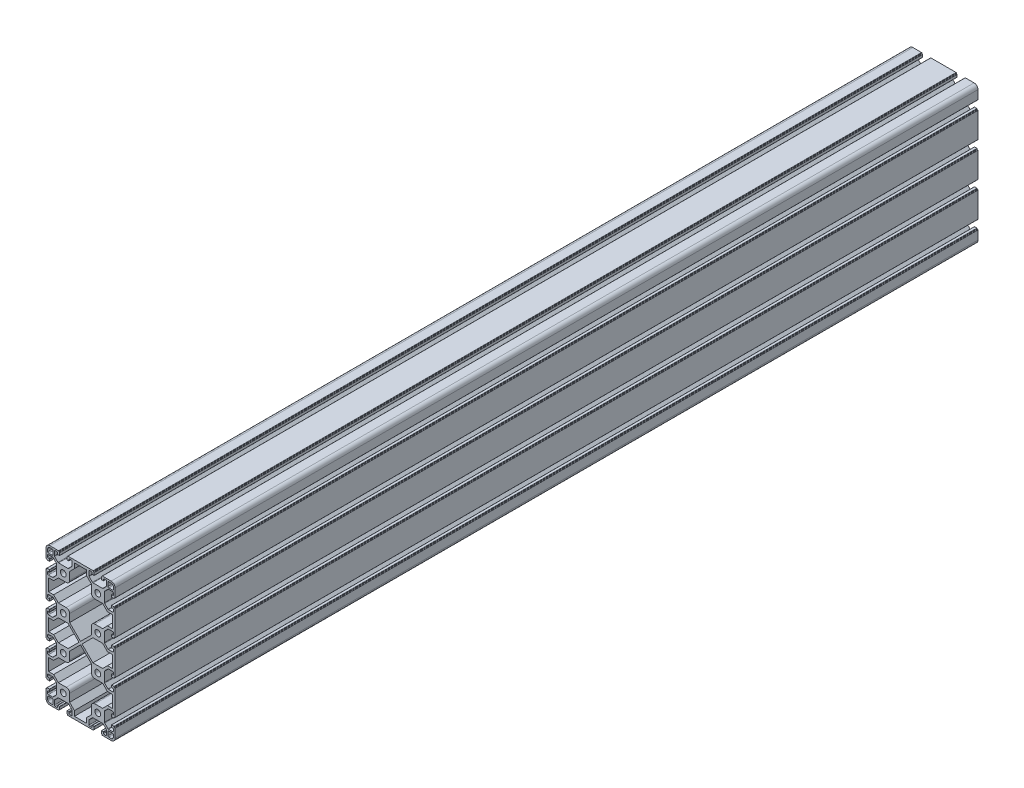
SolidWorks part; units mm, degrees
material "6063 T5"
ref_plane "Спереди" through (0, 0, 0) normal (0, 0, 1) x (1, 0, 0)
ref_plane "Сверху" through (0, 0, 0) normal (0, 1, 0) x (1, 0, 0)
ref_plane "Справа" through (0, 0, 0) normal (1, 0, 0) x (0, 0, -1)
sketch "Эскиз1" plane through (0, 0, 0) normal (0, 0, 1) x (1, 0, 0)
  line L0 (-19.98, 20.5457) -> (20.02, 20.5457) construction
  line L1 (-20, 10.25) -> (-20, 15.5)
  line L2 (-15.5, 20) -> (-10.25, 20)
  line L3 (20, 0) -> (20, 56.8781) construction
  line L4 (-12.8, 11.8) -> (-17, 11.8)
  line L5 (-11.8, 12.8) -> (-11.8, 17)
  line L6 (-12.8, 18) -> (-15.5, 18)
  line L7 (-18, 12.8) -> (-18, 15.5)
  line L20 (0, 0) -> (40, 0) construction
  line L25 (0, 0) -> (0, -120) construction
  line L26 (0, -120) -> (40, -120) construction
  line L31 (40, 0) -> (40, -120) construction
  line L32 (58, 12.8) -> (58, 15.5)
  line L37 (52.8, 18) -> (55.5, 18)
  line L38 (51.8, 12.8) -> (51.8, 17)
  line L43 (52.8, 11.8) -> (57, 11.8)
  line L44 (55.5, 20) -> (50.25, 20)
  line L45 (60, 10.25) -> (60, 15.5)
  line L46 (10.25, 20) -> (29.75, 20)
  line L47 (-20.044, 23.5406) -> (59.956, 23.5406) construction
  line L67 (60, -10.25) -> (60, -50.25) construction
  line L68 (-20, -10.25) -> (-20, -29.75)
  line L72 (-20, -90.25) -> (-20, -109.75)
  line L74 (60, -90.25) -> (60, -109.75)
  line L76 (60, -50.25) -> (60, -69.75)
  line L77 (60, -10.25) -> (60, -29.75)
  line L78 (-20, -50.25) -> (-20, -69.75)
  line L79 (0, -60) -> (23.4541, -60) construction
  line L80 (60, -130.25) -> (60, -135.5)
  line L81 (55.5, -140) -> (50.25, -140)
  line L82 (51.8, -132.8) -> (51.8, -137)
  line L83 (52.8, -131.8) -> (57, -131.8)
  line L84 (58, -132.8) -> (58, -135.5)
  line L85 (52.8, -138) -> (55.5, -138)
  line L86 (10.25, -140) -> (29.75, -140)
  line L87 (-12.8, -138) -> (-15.5, -138)
  line L88 (-18, -132.8) -> (-18, -135.5)
  line L89 (-12.8, -131.8) -> (-17, -131.8)
  line L90 (-11.8, -132.8) -> (-11.8, -137)
  line L91 (-15.5, -140) -> (-10.25, -140)
  line L92 (-20, -130.25) -> (-20, -135.5)
  line L93 (-26.4314, 19.9357) -> (-26.4314, -140.0643) construction
  line L94 (27.0645, 17) -> (12.9355, 17)
  line L95 (12.9355, 17) -> (12.9355, 11.2)
  line L96 (12.9355, 11.2) -> (7.4, 5.6645)
  line L97 (7.4, 5.6645) -> (7.4, -3.4)
  line L98 (3.4, -7.4) -> (-5.6645, -7.4)
  line L99 (-5.6645, -7.4) -> (-11.2, -12.9355)
  line L100 (-11.2, -12.9355) -> (-17, -12.9355)
  line L101 (-17, -12.9355) -> (-17, -27.0645)
  line L102 (-17, -20) -> (21.7241, -20) construction
  line L103 (-11.2, -27.0645) -> (-17, -27.0645)
  line L104 (-5.6645, -32.6) -> (-11.2, -27.0645)
  line L105 (3.4, -32.6) -> (-5.6645, -32.6)
  line L106 (7.4, -45.6645) -> (7.4, -36.6)
  line L107 (7.4, -45.6645) -> (20, -58.2645)
  line L108 (32.6, -45.6645) -> (20, -58.2645)
  line L109 (32.6, -45.6645) -> (32.6, -36.6)
  line L110 (36.6, -32.6) -> (45.6645, -32.6)
  line L111 (45.6645, -32.6) -> (51.2, -27.0645)
  line L112 (51.2, -27.0645) -> (57, -27.0645)
  line L113 (57, -12.9355) -> (57, -27.0645)
  line L114 (51.2, -12.9355) -> (57, -12.9355)
  line L115 (45.6645, -7.4) -> (51.2, -12.9355)
  line L116 (36.6, -7.4) -> (45.6645, -7.4)
  line L117 (32.6, 5.6645) -> (32.6, -3.4)
  line L118 (27.0645, 11.2) -> (32.6, 5.6645)
  line L119 (27.0645, 17) -> (27.0645, 11.2)
  line L120 (18.2645, -60) -> (5.6645, -47.4)
  line L121 (5.6645, -47.4) -> (-5.6645, -47.4)
  line L122 (-5.6645, -47.4) -> (-11.2, -52.9355)
  line L123 (-11.2, -52.9355) -> (-17, -52.9355)
  line L124 (-17, -52.9355) -> (-17, -67.0645)
  line L125 (-11.2, -67.0645) -> (-17, -67.0645)
  line L126 (-5.6645, -72.6) -> (-11.2, -67.0645)
  line L127 (5.6645, -72.6) -> (-5.6645, -72.6)
  line L128 (18.2645, -60) -> (5.6645, -72.6)
  line L129 (21.7355, -60) -> (34.3355, -47.4)
  line L130 (34.3355, -47.4) -> (45.6645, -47.4)
  line L131 (45.6645, -47.4) -> (51.2, -52.9355)
  line L132 (51.2, -52.9355) -> (57, -52.9355)
  line L133 (57, -52.9355) -> (57, -67.0645)
  line L134 (51.2, -67.0645) -> (57, -67.0645)
  line L135 (45.6645, -72.6) -> (51.2, -67.0645)
  line L136 (34.3355, -72.6) -> (45.6645, -72.6)
  line L137 (21.7355, -60) -> (34.3355, -72.6)
  line L138 (51.2, -107.0645) -> (57, -107.0645)
  line L139 (45.6645, -112.6) -> (51.2, -107.0645)
  line L140 (36.6, -112.6) -> (45.6645, -112.6)
  line L141 (32.6, -125.6645) -> (32.6, -116.6)
  line L142 (27.0645, -131.2) -> (32.6, -125.6645)
  line L143 (27.0645, -137) -> (27.0645, -131.2)
  line L144 (27.0645, -137) -> (12.9355, -137)
  line L145 (12.9355, -137) -> (12.9355, -131.2)
  line L146 (12.9355, -131.2) -> (7.4, -125.6645)
  line L147 (7.4, -125.6645) -> (7.4, -116.6)
  line L148 (3.4, -112.6) -> (-5.6645, -112.6)
  line L149 (-5.6645, -112.6) -> (-11.2, -107.0645)
  line L150 (-11.2, -107.0645) -> (-17, -107.0645)
  line L151 (-17, -107.0645) -> (-17, -92.9355)
  line L152 (-11.2, -92.9355) -> (-17, -92.9355)
  line L153 (-5.6645, -87.4) -> (-11.2, -92.9355)
  line L154 (3.4, -87.4) -> (-5.6645, -87.4)
  line L155 (7.4, -74.3355) -> (7.4, -83.4)
  line L156 (7.4, -74.3355) -> (20, -61.7355)
  line L157 (32.6, -74.3355) -> (20, -61.7355)
  line L158 (32.6, -74.3355) -> (32.6, -83.4)
  line L159 (36.6, -87.4) -> (45.6645, -87.4)
  line L160 (45.6645, -87.4) -> (51.2, -92.9355)
  line L161 (51.2, -92.9355) -> (57, -92.9355)
  line L162 (57, -107.0645) -> (57, -92.9355)
  arc A0 (-20, 15.5) -> (-15.5, 20) centre (-15.5, 15.5) cw
  arc A1 (-15.5, 18) -> (-18, 15.5) centre (-15.5, 15.5) ccw
  arc A2 (-17, 11.8) -> (-18, 12.8) centre (-17, 12.8) cw
  arc A3 (-12.8, 11.8) -> (-11.8, 12.8) centre (-12.8, 12.8) ccw
  arc A4 (-11.8, 17) -> (-12.8, 18) centre (-12.8, 17) ccw
  circle A5 centre (0, 0) radius 3.4
  circle A6 centre (40, 0) radius 3.4
  arc A24 (51.8, 17) -> (52.8, 18) centre (52.8, 17) cw
  arc A30 (52.8, 11.8) -> (51.8, 12.8) centre (52.8, 12.8) cw
  arc A40 (57, 11.8) -> (58, 12.8) centre (57, 12.8) ccw
  arc A41 (55.5, 18) -> (58, 15.5) centre (55.5, 15.5) cw
  arc A42 (60, 15.5) -> (55.5, 20) centre (55.5, 15.5) ccw
  circle A43 centre (40, -40) radius 3.4
  circle A44 centre (0, -40) radius 3.4
  circle A45 centre (40, -80) radius 3.4
  circle A46 centre (0, -80) radius 3.4
  circle A47 centre (40, -120) radius 3.4
  circle A48 centre (0, -120) radius 3.4
  arc A49 (60, -135.5) -> (55.5, -140) centre (55.5, -135.5) cw
  arc A50 (52.8, -131.8) -> (51.8, -132.8) centre (52.8, -132.8) ccw
  arc A51 (57, -131.8) -> (58, -132.8) centre (57, -132.8) cw
  arc A52 (55.5, -138) -> (58, -135.5) centre (55.5, -135.5) ccw
  arc A53 (51.8, -137) -> (52.8, -138) centre (52.8, -137) ccw
  arc A54 (-15.5, -138) -> (-18, -135.5) centre (-15.5, -135.5) cw
  arc A55 (-17, -131.8) -> (-18, -132.8) centre (-17, -132.8) ccw
  arc A56 (-12.8, -131.8) -> (-11.8, -132.8) centre (-12.8, -132.8) cw
  arc A57 (-11.8, -137) -> (-12.8, -138) centre (-12.8, -137) cw
  arc A58 (-20, -135.5) -> (-15.5, -140) centre (-15.5, -135.5) ccw
  arc A59 (7.4, -3.4) -> (3.4, -7.4) centre (3.4, -3.4) cw
  arc A60 (7.4, -36.6) -> (3.4, -32.6) centre (3.4, -36.6) ccw
  arc A61 (32.6, -36.6) -> (36.6, -32.6) centre (36.6, -36.6) cw
  arc A62 (32.6, -3.4) -> (36.6, -7.4) centre (36.6, -3.4) ccw
  arc A63 (32.6, -116.6) -> (36.6, -112.6) centre (36.6, -116.6) cw
  arc A64 (7.4, -116.6) -> (3.4, -112.6) centre (3.4, -116.6) ccw
  arc A65 (7.4, -83.4) -> (3.4, -87.4) centre (3.4, -83.4) cw
  arc A66 (32.6, -83.4) -> (36.6, -87.4) centre (36.6, -83.4) ccw
  point P5 (0, 0)
  point P42 (40, 0)
  point P151 (20, 17)
  point P158 (-17, -60)
  line B0 (-20, 10.25) -> (-20, 5.4)
  line B1 (-19.7, 5.1) -> (-19.3, 5.1)
  line B2 (-19, 4.8) -> (-19, 4.4)
  line B3 (-18.7, 4.1) -> (-16, 4.1)
  line B4 (-15.7, 4.4) -> (-15.7, 6.3)
  line B5 (-16, 6.6) -> (-17.2, 6.6)
  line B6 (-18.2, 7.6) -> (-18.2, 9.25)
  line B7 (-17.2, 10.25) -> (-12.4642, 10.25)
  line B8 (-11.7571, 9.9571) -> (-7.9929, 6.1929)
  line B9 (-7.7, 5.4858) -> (-7.7, -5.4858)
  line B10 (-7.7, 0) -> (-20, 0) construction
  line B11 (-11.7571, -9.9571) -> (-7.9929, -6.1929)
  line B12 (-17.2, -10.25) -> (-12.4642, -10.25)
  line B13 (-18.2, -7.6) -> (-18.2, -9.25)
  line B14 (-16, -6.6) -> (-17.2, -6.6)
  line B15 (-15.7, -4.4) -> (-15.7, -6.3)
  line B16 (-18.7, -4.1) -> (-16, -4.1)
  line B17 (-19, -4.8) -> (-19, -4.4)
  line B18 (-19.7, -5.1) -> (-19.3, -5.1)
  line B19 (-20, -10.25) -> (-20, -5.4)
  arc B20 (-15.7, 6.3) -> (-16, 6.6) centre (-16, 6.3) ccw
  arc B21 (-16, 4.1) -> (-15.7, 4.4) centre (-16, 4.4) ccw
  arc B22 (-19, 4.4) -> (-18.7, 4.1) centre (-18.7, 4.4) ccw
  arc B23 (-19.3, 5.1) -> (-19, 4.8) centre (-19.3, 4.8) cw
  arc B24 (-20, 5.4) -> (-19.7, 5.1) centre (-19.7, 5.4) ccw
  arc B25 (-7.9929, 6.1929) -> (-7.7, 5.4858) centre (-8.7, 5.4858) cw
  arc B26 (-12.4642, 10.25) -> (-11.7571, 9.9571) centre (-12.4642, 9.25) cw
  arc B27 (-18.2, 9.25) -> (-17.2, 10.25) centre (-17.2, 9.25) cw
  arc B28 (-17.2, 6.6) -> (-18.2, 7.6) centre (-17.2, 7.6) cw
  arc B29 (-17.2, -6.6) -> (-18.2, -7.6) centre (-17.2, -7.6) ccw
  arc B30 (-18.2, -9.25) -> (-17.2, -10.25) centre (-17.2, -9.25) ccw
  arc B31 (-12.4642, -10.25) -> (-11.7571, -9.9571) centre (-12.4642, -9.25) ccw
  arc B32 (-7.9929, -6.1929) -> (-7.7, -5.4858) centre (-8.7, -5.4858) ccw
  arc B33 (-20, -5.4) -> (-19.7, -5.1) centre (-19.7, -5.4) cw
  arc B34 (-19.3, -5.1) -> (-19, -4.8) centre (-19.3, -4.8) ccw
  arc B35 (-19, -4.4) -> (-18.7, -4.1) centre (-18.7, -4.4) cw
  arc B36 (-16, -4.1) -> (-15.7, -4.4) centre (-16, -4.4) cw
  arc B37 (-15.7, -6.3) -> (-16, -6.6) centre (-16, -6.3) cw
  line B38 (10.25, 20) -> (5.4, 20)
  line B39 (5.1, 19.7) -> (5.1, 19.3)
  line B40 (4.8, 19) -> (4.4, 19)
  line B41 (4.1, 18.7) -> (4.1, 16)
  line B42 (4.4, 15.7) -> (6.3, 15.7)
  line B43 (6.6, 16) -> (6.6, 17.2)
  line B44 (7.6, 18.2) -> (9.25, 18.2)
  line B45 (10.25, 17.2) -> (10.25, 12.4642)
  line B46 (9.9571, 11.7571) -> (6.1929, 7.9929)
  line B47 (5.4858, 7.7) -> (-5.4858, 7.7)
  line B48 (0, 7.7) -> (0, 20) construction
  line B49 (-9.9571, 11.7571) -> (-6.1929, 7.9929)
  line B50 (-10.25, 17.2) -> (-10.25, 12.4642)
  line B51 (-7.6, 18.2) -> (-9.25, 18.2)
  line B52 (-6.6, 16) -> (-6.6, 17.2)
  line B53 (-4.4, 15.7) -> (-6.3, 15.7)
  line B54 (-4.1, 18.7) -> (-4.1, 16)
  line B55 (-4.8, 19) -> (-4.4, 19)
  line B56 (-5.1, 19.7) -> (-5.1, 19.3)
  line B57 (-10.25, 20) -> (-5.4, 20)
  arc B58 (6.3, 15.7) -> (6.6, 16) centre (6.3, 16) ccw
  arc B59 (4.1, 16) -> (4.4, 15.7) centre (4.4, 16) ccw
  arc B60 (4.4, 19) -> (4.1, 18.7) centre (4.4, 18.7) ccw
  arc B61 (5.1, 19.3) -> (4.8, 19) centre (4.8, 19.3) cw
  arc B62 (5.4, 20) -> (5.1, 19.7) centre (5.4, 19.7) ccw
  arc B63 (6.1929, 7.9929) -> (5.4858, 7.7) centre (5.4858, 8.7) cw
  arc B64 (10.25, 12.4642) -> (9.9571, 11.7571) centre (9.25, 12.4642) cw
  arc B65 (9.25, 18.2) -> (10.25, 17.2) centre (9.25, 17.2) cw
  arc B66 (6.6, 17.2) -> (7.6, 18.2) centre (7.6, 17.2) cw
  arc B67 (-6.6, 17.2) -> (-7.6, 18.2) centre (-7.6, 17.2) ccw
  arc B68 (-9.25, 18.2) -> (-10.25, 17.2) centre (-9.25, 17.2) ccw
  arc B69 (-10.25, 12.4642) -> (-9.9571, 11.7571) centre (-9.25, 12.4642) ccw
  arc B70 (-6.1929, 7.9929) -> (-5.4858, 7.7) centre (-5.4858, 8.7) ccw
  arc B71 (-5.4, 20) -> (-5.1, 19.7) centre (-5.4, 19.7) cw
  arc B72 (-5.1, 19.3) -> (-4.8, 19) centre (-4.8, 19.3) ccw
  arc B73 (-4.4, 19) -> (-4.1, 18.7) centre (-4.4, 18.7) cw
  arc B74 (-4.1, 16) -> (-4.4, 15.7) centre (-4.4, 16) cw
  arc B75 (-6.3, 15.7) -> (-6.6, 16) centre (-6.3, 16) cw
  line B76 (29.75, 20) -> (34.6, 20)
  line B77 (34.9, 19.7) -> (34.9, 19.3)
  line B78 (35.2, 19) -> (35.6, 19)
  line B79 (35.9, 18.7) -> (35.9, 16)
  line B80 (35.6, 15.7) -> (33.7, 15.7)
  line B81 (33.4, 16) -> (33.4, 17.2)
  line B82 (32.4, 18.2) -> (30.75, 18.2)
  line B83 (29.75, 17.2) -> (29.75, 12.4642)
  line B84 (30.0429, 11.7571) -> (33.8071, 7.9929)
  line B85 (34.5142, 7.7) -> (45.4858, 7.7)
  line B86 (40, 7.7) -> (40, 20) construction
  line B87 (49.9571, 11.7571) -> (46.1929, 7.9929)
  line B88 (50.25, 17.2) -> (50.25, 12.4642)
  line B89 (47.6, 18.2) -> (49.25, 18.2)
  line B90 (46.6, 16) -> (46.6, 17.2)
  line B91 (44.4, 15.7) -> (46.3, 15.7)
  line B92 (44.1, 18.7) -> (44.1, 16)
  line B93 (44.8, 19) -> (44.4, 19)
  line B94 (45.1, 19.7) -> (45.1, 19.3)
  line B95 (50.25, 20) -> (45.4, 20)
  arc B96 (33.7, 15.7) -> (33.4, 16) centre (33.7, 16) cw
  arc B97 (35.9, 16) -> (35.6, 15.7) centre (35.6, 16) cw
  arc B98 (35.6, 19) -> (35.9, 18.7) centre (35.6, 18.7) cw
  arc B99 (34.9, 19.3) -> (35.2, 19) centre (35.2, 19.3) ccw
  arc B100 (34.6, 20) -> (34.9, 19.7) centre (34.6, 19.7) cw
  arc B101 (33.8071, 7.9929) -> (34.5142, 7.7) centre (34.5142, 8.7) ccw
  arc B102 (29.75, 12.4642) -> (30.0429, 11.7571) centre (30.75, 12.4642) ccw
  arc B103 (30.75, 18.2) -> (29.75, 17.2) centre (30.75, 17.2) ccw
  arc B104 (33.4, 17.2) -> (32.4, 18.2) centre (32.4, 17.2) ccw
  arc B105 (46.6, 17.2) -> (47.6, 18.2) centre (47.6, 17.2) cw
  arc B106 (49.25, 18.2) -> (50.25, 17.2) centre (49.25, 17.2) cw
  arc B107 (50.25, 12.4642) -> (49.9571, 11.7571) centre (49.25, 12.4642) cw
  arc B108 (46.1929, 7.9929) -> (45.4858, 7.7) centre (45.4858, 8.7) cw
  arc B109 (45.4, 20) -> (45.1, 19.7) centre (45.4, 19.7) ccw
  arc B110 (45.1, 19.3) -> (44.8, 19) centre (44.8, 19.3) cw
  arc B111 (44.4, 19) -> (44.1, 18.7) centre (44.4, 18.7) ccw
  arc B112 (44.1, 16) -> (44.4, 15.7) centre (44.4, 16) ccw
  arc B113 (46.3, 15.7) -> (46.6, 16) centre (46.3, 16) ccw
  line B114 (60, 10.25) -> (60, 5.4)
  line B115 (59.7, 5.1) -> (59.3, 5.1)
  line B116 (59, 4.8) -> (59, 4.4)
  line B117 (58.7, 4.1) -> (56, 4.1)
  line B118 (55.7, 4.4) -> (55.7, 6.3)
  line B119 (56, 6.6) -> (57.2, 6.6)
  line B120 (58.2, 7.6) -> (58.2, 9.25)
  line B121 (57.2, 10.25) -> (52.4642, 10.25)
  line B122 (51.7571, 9.9571) -> (47.9929, 6.1929)
  line B123 (47.7, 5.4858) -> (47.7, -5.4858)
  line B124 (47.7, 0) -> (60, 0) construction
  line B125 (51.7571, -9.9571) -> (47.9929, -6.1929)
  line B126 (57.2, -10.25) -> (52.4642, -10.25)
  line B127 (58.2, -7.6) -> (58.2, -9.25)
  line B128 (56, -6.6) -> (57.2, -6.6)
  line B129 (55.7, -4.4) -> (55.7, -6.3)
  line B130 (58.7, -4.1) -> (56, -4.1)
  line B131 (59, -4.8) -> (59, -4.4)
  line B132 (59.7, -5.1) -> (59.3, -5.1)
  line B133 (60, -10.25) -> (60, -5.4)
  arc B134 (55.7, 6.3) -> (56, 6.6) centre (56, 6.3) cw
  arc B135 (56, 4.1) -> (55.7, 4.4) centre (56, 4.4) cw
  arc B136 (59, 4.4) -> (58.7, 4.1) centre (58.7, 4.4) cw
  arc B137 (59.3, 5.1) -> (59, 4.8) centre (59.3, 4.8) ccw
  arc B138 (60, 5.4) -> (59.7, 5.1) centre (59.7, 5.4) cw
  arc B139 (47.9929, 6.1929) -> (47.7, 5.4858) centre (48.7, 5.4858) ccw
  arc B140 (52.4642, 10.25) -> (51.7571, 9.9571) centre (52.4642, 9.25) ccw
  arc B141 (58.2, 9.25) -> (57.2, 10.25) centre (57.2, 9.25) ccw
  arc B142 (57.2, 6.6) -> (58.2, 7.6) centre (57.2, 7.6) ccw
  arc B143 (57.2, -6.6) -> (58.2, -7.6) centre (57.2, -7.6) cw
  arc B144 (58.2, -9.25) -> (57.2, -10.25) centre (57.2, -9.25) cw
  arc B145 (52.4642, -10.25) -> (51.7571, -9.9571) centre (52.4642, -9.25) cw
  arc B146 (47.9929, -6.1929) -> (47.7, -5.4858) centre (48.7, -5.4858) cw
  arc B147 (60, -5.4) -> (59.7, -5.1) centre (59.7, -5.4) ccw
  arc B148 (59.3, -5.1) -> (59, -4.8) centre (59.3, -4.8) cw
  arc B149 (59, -4.4) -> (58.7, -4.1) centre (58.7, -4.4) ccw
  arc B150 (56, -4.1) -> (55.7, -4.4) centre (56, -4.4) ccw
  arc B151 (55.7, -6.3) -> (56, -6.6) centre (56, -6.3) ccw
  line B152 (60, -29.75) -> (60, -34.6)
  line B153 (59.7, -34.9) -> (59.3, -34.9)
  line B154 (59, -35.2) -> (59, -35.6)
  line B155 (58.7, -35.9) -> (56, -35.9)
  line B156 (55.7, -35.6) -> (55.7, -33.7)
  line B157 (56, -33.4) -> (57.2, -33.4)
  line B158 (58.2, -32.4) -> (58.2, -30.75)
  line B159 (57.2, -29.75) -> (52.4642, -29.75)
  line B160 (51.7571, -30.0429) -> (47.9929, -33.8071)
  line B161 (47.7, -34.5142) -> (47.7, -45.4858)
  line B162 (47.7, -40) -> (60, -40) construction
  line B163 (51.7571, -49.9571) -> (47.9929, -46.1929)
  line B164 (57.2, -50.25) -> (52.4642, -50.25)
  line B165 (58.2, -47.6) -> (58.2, -49.25)
  line B166 (56, -46.6) -> (57.2, -46.6)
  line B167 (55.7, -44.4) -> (55.7, -46.3)
  line B168 (58.7, -44.1) -> (56, -44.1)
  line B169 (59, -44.8) -> (59, -44.4)
  line B170 (59.7, -45.1) -> (59.3, -45.1)
  line B171 (60, -50.25) -> (60, -45.4)
  arc B172 (55.7, -33.7) -> (56, -33.4) centre (56, -33.7) cw
  arc B173 (56, -35.9) -> (55.7, -35.6) centre (56, -35.6) cw
  arc B174 (59, -35.6) -> (58.7, -35.9) centre (58.7, -35.6) cw
  arc B175 (59.3, -34.9) -> (59, -35.2) centre (59.3, -35.2) ccw
  arc B176 (60, -34.6) -> (59.7, -34.9) centre (59.7, -34.6) cw
  arc B177 (47.9929, -33.8071) -> (47.7, -34.5142) centre (48.7, -34.5142) ccw
  arc B178 (52.4642, -29.75) -> (51.7571, -30.0429) centre (52.4642, -30.75) ccw
  arc B179 (58.2, -30.75) -> (57.2, -29.75) centre (57.2, -30.75) ccw
  arc B180 (57.2, -33.4) -> (58.2, -32.4) centre (57.2, -32.4) ccw
  arc B181 (57.2, -46.6) -> (58.2, -47.6) centre (57.2, -47.6) cw
  arc B182 (58.2, -49.25) -> (57.2, -50.25) centre (57.2, -49.25) cw
  arc B183 (52.4642, -50.25) -> (51.7571, -49.9571) centre (52.4642, -49.25) cw
  arc B184 (47.9929, -46.1929) -> (47.7, -45.4858) centre (48.7, -45.4858) cw
  arc B185 (60, -45.4) -> (59.7, -45.1) centre (59.7, -45.4) ccw
  arc B186 (59.3, -45.1) -> (59, -44.8) centre (59.3, -44.8) cw
  arc B187 (59, -44.4) -> (58.7, -44.1) centre (58.7, -44.4) ccw
  arc B188 (56, -44.1) -> (55.7, -44.4) centre (56, -44.4) ccw
  arc B189 (55.7, -46.3) -> (56, -46.6) centre (56, -46.3) ccw
  line B190 (-20, -29.75) -> (-20, -34.6)
  line B191 (-19.7, -34.9) -> (-19.3, -34.9)
  line B192 (-19, -35.2) -> (-19, -35.6)
  line B193 (-18.7, -35.9) -> (-16, -35.9)
  line B194 (-15.7, -35.6) -> (-15.7, -33.7)
  line B195 (-16, -33.4) -> (-17.2, -33.4)
  line B196 (-18.2, -32.4) -> (-18.2, -30.75)
  line B197 (-17.2, -29.75) -> (-12.4642, -29.75)
  line B198 (-11.7571, -30.0429) -> (-7.9929, -33.8071)
  line B199 (-7.7, -34.5142) -> (-7.7, -45.4858)
  line B200 (-7.7, -40) -> (-20, -40) construction
  line B201 (-11.7571, -49.9571) -> (-7.9929, -46.1929)
  line B202 (-17.2, -50.25) -> (-12.4642, -50.25)
  line B203 (-18.2, -47.6) -> (-18.2, -49.25)
  line B204 (-16, -46.6) -> (-17.2, -46.6)
  line B205 (-15.7, -44.4) -> (-15.7, -46.3)
  line B206 (-18.7, -44.1) -> (-16, -44.1)
  line B207 (-19, -44.8) -> (-19, -44.4)
  line B208 (-19.7, -45.1) -> (-19.3, -45.1)
  line B209 (-20, -50.25) -> (-20, -45.4)
  arc B210 (-15.7, -33.7) -> (-16, -33.4) centre (-16, -33.7) ccw
  arc B211 (-16, -35.9) -> (-15.7, -35.6) centre (-16, -35.6) ccw
  arc B212 (-19, -35.6) -> (-18.7, -35.9) centre (-18.7, -35.6) ccw
  arc B213 (-19.3, -34.9) -> (-19, -35.2) centre (-19.3, -35.2) cw
  arc B214 (-20, -34.6) -> (-19.7, -34.9) centre (-19.7, -34.6) ccw
  arc B215 (-7.9929, -33.8071) -> (-7.7, -34.5142) centre (-8.7, -34.5142) cw
  arc B216 (-12.4642, -29.75) -> (-11.7571, -30.0429) centre (-12.4642, -30.75) cw
  arc B217 (-18.2, -30.75) -> (-17.2, -29.75) centre (-17.2, -30.75) cw
  arc B218 (-17.2, -33.4) -> (-18.2, -32.4) centre (-17.2, -32.4) cw
  arc B219 (-17.2, -46.6) -> (-18.2, -47.6) centre (-17.2, -47.6) ccw
  arc B220 (-18.2, -49.25) -> (-17.2, -50.25) centre (-17.2, -49.25) ccw
  arc B221 (-12.4642, -50.25) -> (-11.7571, -49.9571) centre (-12.4642, -49.25) ccw
  arc B222 (-7.9929, -46.1929) -> (-7.7, -45.4858) centre (-8.7, -45.4858) ccw
  arc B223 (-20, -45.4) -> (-19.7, -45.1) centre (-19.7, -45.4) cw
  arc B224 (-19.3, -45.1) -> (-19, -44.8) centre (-19.3, -44.8) ccw
  arc B225 (-19, -44.4) -> (-18.7, -44.1) centre (-18.7, -44.4) cw
  arc B226 (-16, -44.1) -> (-15.7, -44.4) centre (-16, -44.4) cw
  arc B227 (-15.7, -46.3) -> (-16, -46.6) centre (-16, -46.3) cw
  line B228 (60, -69.75) -> (60, -74.6)
  line B229 (59.7, -74.9) -> (59.3, -74.9)
  line B230 (59, -75.2) -> (59, -75.6)
  line B231 (58.7, -75.9) -> (56, -75.9)
  line B232 (55.7, -75.6) -> (55.7, -73.7)
  line B233 (56, -73.4) -> (57.2, -73.4)
  line B234 (58.2, -72.4) -> (58.2, -70.75)
  line B235 (57.2, -69.75) -> (52.4642, -69.75)
  line B236 (51.7571, -70.0429) -> (47.9929, -73.8071)
  line B237 (47.7, -74.5142) -> (47.7, -85.4858)
  line B238 (47.7, -80) -> (60, -80) construction
  line B239 (51.7571, -89.9571) -> (47.9929, -86.1929)
  line B240 (57.2, -90.25) -> (52.4642, -90.25)
  line B241 (58.2, -87.6) -> (58.2, -89.25)
  line B242 (56, -86.6) -> (57.2, -86.6)
  line B243 (55.7, -84.4) -> (55.7, -86.3)
  line B244 (58.7, -84.1) -> (56, -84.1)
  line B245 (59, -84.8) -> (59, -84.4)
  line B246 (59.7, -85.1) -> (59.3, -85.1)
  line B247 (60, -90.25) -> (60, -85.4)
  arc B248 (55.7, -73.7) -> (56, -73.4) centre (56, -73.7) cw
  arc B249 (56, -75.9) -> (55.7, -75.6) centre (56, -75.6) cw
  arc B250 (59, -75.6) -> (58.7, -75.9) centre (58.7, -75.6) cw
  arc B251 (59.3, -74.9) -> (59, -75.2) centre (59.3, -75.2) ccw
  arc B252 (60, -74.6) -> (59.7, -74.9) centre (59.7, -74.6) cw
  arc B253 (47.9929, -73.8071) -> (47.7, -74.5142) centre (48.7, -74.5142) ccw
  arc B254 (52.4642, -69.75) -> (51.7571, -70.0429) centre (52.4642, -70.75) ccw
  arc B255 (58.2, -70.75) -> (57.2, -69.75) centre (57.2, -70.75) ccw
  arc B256 (57.2, -73.4) -> (58.2, -72.4) centre (57.2, -72.4) ccw
  arc B257 (57.2, -86.6) -> (58.2, -87.6) centre (57.2, -87.6) cw
  arc B258 (58.2, -89.25) -> (57.2, -90.25) centre (57.2, -89.25) cw
  arc B259 (52.4642, -90.25) -> (51.7571, -89.9571) centre (52.4642, -89.25) cw
  arc B260 (47.9929, -86.1929) -> (47.7, -85.4858) centre (48.7, -85.4858) cw
  arc B261 (60, -85.4) -> (59.7, -85.1) centre (59.7, -85.4) ccw
  arc B262 (59.3, -85.1) -> (59, -84.8) centre (59.3, -84.8) cw
  arc B263 (59, -84.4) -> (58.7, -84.1) centre (58.7, -84.4) ccw
  arc B264 (56, -84.1) -> (55.7, -84.4) centre (56, -84.4) ccw
  arc B265 (55.7, -86.3) -> (56, -86.6) centre (56, -86.3) ccw
  line B266 (-20, -69.75) -> (-20, -74.6)
  line B267 (-19.7, -74.9) -> (-19.3, -74.9)
  line B268 (-19, -75.2) -> (-19, -75.6)
  line B269 (-18.7, -75.9) -> (-16, -75.9)
  line B270 (-15.7, -75.6) -> (-15.7, -73.7)
  line B271 (-16, -73.4) -> (-17.2, -73.4)
  line B272 (-18.2, -72.4) -> (-18.2, -70.75)
  line B273 (-17.2, -69.75) -> (-12.4642, -69.75)
  line B274 (-11.7571, -70.0429) -> (-7.9929, -73.8071)
  line B275 (-7.7, -74.5142) -> (-7.7, -85.4858)
  line B276 (-7.7, -80) -> (-20, -80) construction
  line B277 (-11.7571, -89.9571) -> (-7.9929, -86.1929)
  line B278 (-17.2, -90.25) -> (-12.4642, -90.25)
  line B279 (-18.2, -87.6) -> (-18.2, -89.25)
  line B280 (-16, -86.6) -> (-17.2, -86.6)
  line B281 (-15.7, -84.4) -> (-15.7, -86.3)
  line B282 (-18.7, -84.1) -> (-16, -84.1)
  line B283 (-19, -84.8) -> (-19, -84.4)
  line B284 (-19.7, -85.1) -> (-19.3, -85.1)
  line B285 (-20, -90.25) -> (-20, -85.4)
  arc B286 (-15.7, -73.7) -> (-16, -73.4) centre (-16, -73.7) ccw
  arc B287 (-16, -75.9) -> (-15.7, -75.6) centre (-16, -75.6) ccw
  arc B288 (-19, -75.6) -> (-18.7, -75.9) centre (-18.7, -75.6) ccw
  arc B289 (-19.3, -74.9) -> (-19, -75.2) centre (-19.3, -75.2) cw
  arc B290 (-20, -74.6) -> (-19.7, -74.9) centre (-19.7, -74.6) ccw
  arc B291 (-7.9929, -73.8071) -> (-7.7, -74.5142) centre (-8.7, -74.5142) cw
  arc B292 (-12.4642, -69.75) -> (-11.7571, -70.0429) centre (-12.4642, -70.75) cw
  arc B293 (-18.2, -70.75) -> (-17.2, -69.75) centre (-17.2, -70.75) cw
  arc B294 (-17.2, -73.4) -> (-18.2, -72.4) centre (-17.2, -72.4) cw
  arc B295 (-17.2, -86.6) -> (-18.2, -87.6) centre (-17.2, -87.6) ccw
  arc B296 (-18.2, -89.25) -> (-17.2, -90.25) centre (-17.2, -89.25) ccw
  arc B297 (-12.4642, -90.25) -> (-11.7571, -89.9571) centre (-12.4642, -89.25) ccw
  arc B298 (-7.9929, -86.1929) -> (-7.7, -85.4858) centre (-8.7, -85.4858) ccw
  arc B299 (-20, -85.4) -> (-19.7, -85.1) centre (-19.7, -85.4) cw
  arc B300 (-19.3, -85.1) -> (-19, -84.8) centre (-19.3, -84.8) ccw
  arc B301 (-19, -84.4) -> (-18.7, -84.1) centre (-18.7, -84.4) cw
  arc B302 (-16, -84.1) -> (-15.7, -84.4) centre (-16, -84.4) cw
  arc B303 (-15.7, -86.3) -> (-16, -86.6) centre (-16, -86.3) cw
  line B304 (60, -109.75) -> (60, -114.6)
  line B305 (59.7, -114.9) -> (59.3, -114.9)
  line B306 (59, -115.2) -> (59, -115.6)
  line B307 (58.7, -115.9) -> (56, -115.9)
  line B308 (55.7, -115.6) -> (55.7, -113.7)
  line B309 (56, -113.4) -> (57.2, -113.4)
  line B310 (58.2, -112.4) -> (58.2, -110.75)
  line B311 (57.2, -109.75) -> (52.4642, -109.75)
  line B312 (51.7571, -110.0429) -> (47.9929, -113.8071)
  line B313 (47.7, -114.5142) -> (47.7, -125.4858)
  line B314 (47.7, -120) -> (60, -120) construction
  line B315 (51.7571, -129.9571) -> (47.9929, -126.1929)
  line B316 (57.2, -130.25) -> (52.4642, -130.25)
  line B317 (58.2, -127.6) -> (58.2, -129.25)
  line B318 (56, -126.6) -> (57.2, -126.6)
  line B319 (55.7, -124.4) -> (55.7, -126.3)
  line B320 (58.7, -124.1) -> (56, -124.1)
  line B321 (59, -124.8) -> (59, -124.4)
  line B322 (59.7, -125.1) -> (59.3, -125.1)
  line B323 (60, -130.25) -> (60, -125.4)
  arc B324 (55.7, -113.7) -> (56, -113.4) centre (56, -113.7) cw
  arc B325 (56, -115.9) -> (55.7, -115.6) centre (56, -115.6) cw
  arc B326 (59, -115.6) -> (58.7, -115.9) centre (58.7, -115.6) cw
  arc B327 (59.3, -114.9) -> (59, -115.2) centre (59.3, -115.2) ccw
  arc B328 (60, -114.6) -> (59.7, -114.9) centre (59.7, -114.6) cw
  arc B329 (47.9929, -113.8071) -> (47.7, -114.5142) centre (48.7, -114.5142) ccw
  arc B330 (52.4642, -109.75) -> (51.7571, -110.0429) centre (52.4642, -110.75) ccw
  arc B331 (58.2, -110.75) -> (57.2, -109.75) centre (57.2, -110.75) ccw
  arc B332 (57.2, -113.4) -> (58.2, -112.4) centre (57.2, -112.4) ccw
  arc B333 (57.2, -126.6) -> (58.2, -127.6) centre (57.2, -127.6) cw
  arc B334 (58.2, -129.25) -> (57.2, -130.25) centre (57.2, -129.25) cw
  arc B335 (52.4642, -130.25) -> (51.7571, -129.9571) centre (52.4642, -129.25) cw
  arc B336 (47.9929, -126.1929) -> (47.7, -125.4858) centre (48.7, -125.4858) cw
  arc B337 (60, -125.4) -> (59.7, -125.1) centre (59.7, -125.4) ccw
  arc B338 (59.3, -125.1) -> (59, -124.8) centre (59.3, -124.8) cw
  arc B339 (59, -124.4) -> (58.7, -124.1) centre (58.7, -124.4) ccw
  arc B340 (56, -124.1) -> (55.7, -124.4) centre (56, -124.4) ccw
  arc B341 (55.7, -126.3) -> (56, -126.6) centre (56, -126.3) ccw
  line B342 (-20, -109.75) -> (-20, -114.6)
  line B343 (-19.7, -114.9) -> (-19.3, -114.9)
  line B344 (-19, -115.2) -> (-19, -115.6)
  line B345 (-18.7, -115.9) -> (-16, -115.9)
  line B346 (-15.7, -115.6) -> (-15.7, -113.7)
  line B347 (-16, -113.4) -> (-17.2, -113.4)
  line B348 (-18.2, -112.4) -> (-18.2, -110.75)
  line B349 (-17.2, -109.75) -> (-12.4642, -109.75)
  line B350 (-11.7571, -110.0429) -> (-7.9929, -113.8071)
  line B351 (-7.7, -114.5142) -> (-7.7, -125.4858)
  line B352 (-7.7, -120) -> (-20, -120) construction
  line B353 (-11.7571, -129.9571) -> (-7.9929, -126.1929)
  line B354 (-17.2, -130.25) -> (-12.4642, -130.25)
  line B355 (-18.2, -127.6) -> (-18.2, -129.25)
  line B356 (-16, -126.6) -> (-17.2, -126.6)
  line B357 (-15.7, -124.4) -> (-15.7, -126.3)
  line B358 (-18.7, -124.1) -> (-16, -124.1)
  line B359 (-19, -124.8) -> (-19, -124.4)
  line B360 (-19.7, -125.1) -> (-19.3, -125.1)
  line B361 (-20, -130.25) -> (-20, -125.4)
  arc B362 (-15.7, -113.7) -> (-16, -113.4) centre (-16, -113.7) ccw
  arc B363 (-16, -115.9) -> (-15.7, -115.6) centre (-16, -115.6) ccw
  arc B364 (-19, -115.6) -> (-18.7, -115.9) centre (-18.7, -115.6) ccw
  arc B365 (-19.3, -114.9) -> (-19, -115.2) centre (-19.3, -115.2) cw
  arc B366 (-20, -114.6) -> (-19.7, -114.9) centre (-19.7, -114.6) ccw
  arc B367 (-7.9929, -113.8071) -> (-7.7, -114.5142) centre (-8.7, -114.5142) cw
  arc B368 (-12.4642, -109.75) -> (-11.7571, -110.0429) centre (-12.4642, -110.75) cw
  arc B369 (-18.2, -110.75) -> (-17.2, -109.75) centre (-17.2, -110.75) cw
  arc B370 (-17.2, -113.4) -> (-18.2, -112.4) centre (-17.2, -112.4) cw
  arc B371 (-17.2, -126.6) -> (-18.2, -127.6) centre (-17.2, -127.6) ccw
  arc B372 (-18.2, -129.25) -> (-17.2, -130.25) centre (-17.2, -129.25) ccw
  arc B373 (-12.4642, -130.25) -> (-11.7571, -129.9571) centre (-12.4642, -129.25) ccw
  arc B374 (-7.9929, -126.1929) -> (-7.7, -125.4858) centre (-8.7, -125.4858) ccw
  arc B375 (-20, -125.4) -> (-19.7, -125.1) centre (-19.7, -125.4) cw
  arc B376 (-19.3, -125.1) -> (-19, -124.8) centre (-19.3, -124.8) ccw
  arc B377 (-19, -124.4) -> (-18.7, -124.1) centre (-18.7, -124.4) cw
  arc B378 (-16, -124.1) -> (-15.7, -124.4) centre (-16, -124.4) cw
  arc B379 (-15.7, -126.3) -> (-16, -126.6) centre (-16, -126.3) cw
  line B380 (29.75, -140) -> (34.6, -140)
  line B381 (34.9, -139.7) -> (34.9, -139.3)
  line B382 (35.2, -139) -> (35.6, -139)
  line B383 (35.9, -138.7) -> (35.9, -136)
  line B384 (35.6, -135.7) -> (33.7, -135.7)
  line B385 (33.4, -136) -> (33.4, -137.2)
  line B386 (32.4, -138.2) -> (30.75, -138.2)
  line B387 (29.75, -137.2) -> (29.75, -132.4642)
  line B388 (30.0429, -131.7571) -> (33.8071, -127.9929)
  line B389 (34.5142, -127.7) -> (45.4858, -127.7)
  line B390 (40, -127.7) -> (40, -140) construction
  line B391 (49.9571, -131.7571) -> (46.1929, -127.9929)
  line B392 (50.25, -137.2) -> (50.25, -132.4642)
  line B393 (47.6, -138.2) -> (49.25, -138.2)
  line B394 (46.6, -136) -> (46.6, -137.2)
  line B395 (44.4, -135.7) -> (46.3, -135.7)
  line B396 (44.1, -138.7) -> (44.1, -136)
  line B397 (44.8, -139) -> (44.4, -139)
  line B398 (45.1, -139.7) -> (45.1, -139.3)
  line B399 (50.25, -140) -> (45.4, -140)
  arc B400 (33.7, -135.7) -> (33.4, -136) centre (33.7, -136) ccw
  arc B401 (35.9, -136) -> (35.6, -135.7) centre (35.6, -136) ccw
  arc B402 (35.6, -139) -> (35.9, -138.7) centre (35.6, -138.7) ccw
  arc B403 (34.9, -139.3) -> (35.2, -139) centre (35.2, -139.3) cw
  arc B404 (34.6, -140) -> (34.9, -139.7) centre (34.6, -139.7) ccw
  arc B405 (33.8071, -127.9929) -> (34.5142, -127.7) centre (34.5142, -128.7) cw
  arc B406 (29.75, -132.4642) -> (30.0429, -131.7571) centre (30.75, -132.4642) cw
  arc B407 (30.75, -138.2) -> (29.75, -137.2) centre (30.75, -137.2) cw
  arc B408 (33.4, -137.2) -> (32.4, -138.2) centre (32.4, -137.2) cw
  arc B409 (46.6, -137.2) -> (47.6, -138.2) centre (47.6, -137.2) ccw
  arc B410 (49.25, -138.2) -> (50.25, -137.2) centre (49.25, -137.2) ccw
  arc B411 (50.25, -132.4642) -> (49.9571, -131.7571) centre (49.25, -132.4642) ccw
  arc B412 (46.1929, -127.9929) -> (45.4858, -127.7) centre (45.4858, -128.7) ccw
  arc B413 (45.4, -140) -> (45.1, -139.7) centre (45.4, -139.7) cw
  arc B414 (45.1, -139.3) -> (44.8, -139) centre (44.8, -139.3) ccw
  arc B415 (44.4, -139) -> (44.1, -138.7) centre (44.4, -138.7) cw
  arc B416 (44.1, -136) -> (44.4, -135.7) centre (44.4, -136) cw
  arc B417 (46.3, -135.7) -> (46.6, -136) centre (46.3, -136) cw
  line B418 (10.25, -140) -> (5.4, -140)
  line B419 (5.1, -139.7) -> (5.1, -139.3)
  line B420 (4.8, -139) -> (4.4, -139)
  line B421 (4.1, -138.7) -> (4.1, -136)
  line B422 (4.4, -135.7) -> (6.3, -135.7)
  line B423 (6.6, -136) -> (6.6, -137.2)
  line B424 (7.6, -138.2) -> (9.25, -138.2)
  line B425 (10.25, -137.2) -> (10.25, -132.4642)
  line B426 (9.9571, -131.7571) -> (6.1929, -127.9929)
  line B427 (5.4858, -127.7) -> (-5.4858, -127.7)
  line B428 (0, -127.7) -> (0, -140) construction
  line B429 (-9.9571, -131.7571) -> (-6.1929, -127.9929)
  line B430 (-10.25, -137.2) -> (-10.25, -132.4642)
  line B431 (-7.6, -138.2) -> (-9.25, -138.2)
  line B432 (-6.6, -136) -> (-6.6, -137.2)
  line B433 (-4.4, -135.7) -> (-6.3, -135.7)
  line B434 (-4.1, -138.7) -> (-4.1, -136)
  line B435 (-4.8, -139) -> (-4.4, -139)
  line B436 (-5.1, -139.7) -> (-5.1, -139.3)
  line B437 (-10.25, -140) -> (-5.4, -140)
  arc B438 (6.3, -135.7) -> (6.6, -136) centre (6.3, -136) cw
  arc B439 (4.1, -136) -> (4.4, -135.7) centre (4.4, -136) cw
  arc B440 (4.4, -139) -> (4.1, -138.7) centre (4.4, -138.7) cw
  arc B441 (5.1, -139.3) -> (4.8, -139) centre (4.8, -139.3) ccw
  arc B442 (5.4, -140) -> (5.1, -139.7) centre (5.4, -139.7) cw
  arc B443 (6.1929, -127.9929) -> (5.4858, -127.7) centre (5.4858, -128.7) ccw
  arc B444 (10.25, -132.4642) -> (9.9571, -131.7571) centre (9.25, -132.4642) ccw
  arc B445 (9.25, -138.2) -> (10.25, -137.2) centre (9.25, -137.2) ccw
  arc B446 (6.6, -137.2) -> (7.6, -138.2) centre (7.6, -137.2) ccw
  arc B447 (-6.6, -137.2) -> (-7.6, -138.2) centre (-7.6, -137.2) cw
  arc B448 (-9.25, -138.2) -> (-10.25, -137.2) centre (-9.25, -137.2) cw
  arc B449 (-10.25, -132.4642) -> (-9.9571, -131.7571) centre (-9.25, -132.4642) cw
  arc B450 (-6.1929, -127.9929) -> (-5.4858, -127.7) centre (-5.4858, -128.7) cw
  arc B451 (-5.4, -140) -> (-5.1, -139.7) centre (-5.4, -139.7) ccw
  arc B452 (-5.1, -139.3) -> (-4.8, -139) centre (-4.8, -139.3) cw
  arc B453 (-4.4, -139) -> (-4.1, -138.7) centre (-4.4, -138.7) ccw
  arc B454 (-4.1, -136) -> (-4.4, -135.7) centre (-4.4, -136) ccw
  arc B455 (-6.3, -135.7) -> (-6.6, -136) centre (-6.3, -136) ccw
  dimension "D12" = 160
  dimension "D13" = 3
  dimension "D2" = 4.5
  dimension "D3" = 2.5
  dimension "D5" = 1
  dimension "D6" = 6.8
  dimension "D15" = 4
  dimension "D1" = 20
  dimension "D4" = 6.2
  dimension "D7" = 40
  dimension "D8" = 80
  dimension "D9" = 120
  dimension "D10" = 4
  dimension "D11" = 40
  dimension "D14" = 2.5
  dimension "D16" = 5.8
  dimension "D17" = 2.5
  dimension "D18" = 7.4
  dimension "D19" = 7.4
  dimension "D20" = 20
  dimension "D21" = 135
  dimension "D22" = 7.4
sketch_block_instance "8B(20,5PL)-1"
sketch_block "8B(20,5PL)" parameters "D7"=0.3, "D8"=1, "D1"=12.3, "D2"=4.3, "D3"=8.2, "D4"=20.5, "D5"=10.2, "D6"=135
sketch_block_instance "8B(20,5PL)-3"
sketch_block_instance "8B(20,5PL)-6"
sketch_block_instance "8B(20,5PL)-7"
sketch_block_instance "8B(20,5PL)-22"
sketch_block_instance "8B(20,5PL)-23"
sketch_block_instance "8B(20,5PL)-24"
sketch_block_instance "8B(20,5PL)-25"
sketch_block_instance "8B(20,5PL)-26"
sketch_block_instance "8B(20,5PL)-27"
sketch_block_instance "8B(20,5PL)-28"
sketch_block_instance "8B(20,5PL)-29"
sketch_block_instance "8B(20,5PL)-32"
sketch_block_instance "8B(20,5PL)-33"
extrude "Бобышка-Вытянуть1" add sketch "Эскиз1" along normal blind 1000 contours B433 B455 B432 B447 B431 B448 B430 B449 B429 B450 B427 B443 B426 B444 B425 B445 B424 B446 B423 B438 B422 B439 B421 B440 B420 B441 B419 B442 B418 L86 B380 B404 B381 B403 B382 B402 B383 B401 B384 B400 B385 B408 B386 B407 B387 B406 B388 B405 B389 B412 B391
